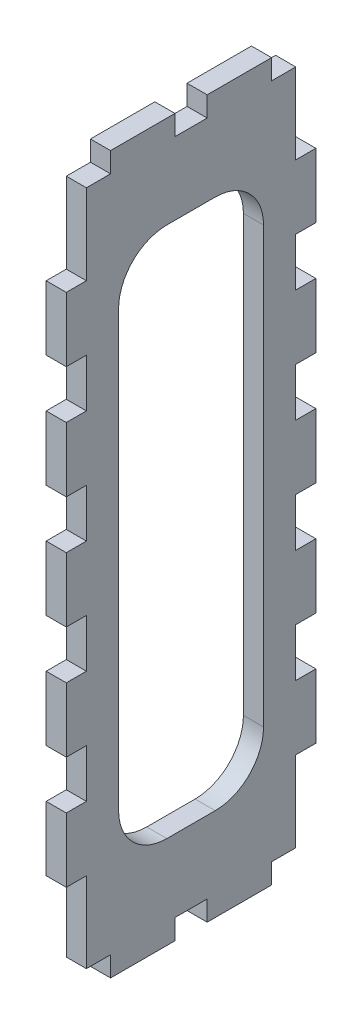
SolidWorks part; units mm, degrees
ref_plane "Front Plane" through (0, 0, 0) normal (0, 0, 1) x (1, 0, 0)
ref_plane "Top Plane" through (0, 0, 0) normal (0, 1, 0) x (1, 0, 0)
ref_plane "Right Plane" through (0, 0, 0) normal (1, 0, 0) x (0, 0, -1)
sketch "Sketch1" plane through (0, 0, 0) normal (1, 0, 0) x (0, 0, -1)
  line L0 (4.0513, 39.2766) -> (-3.5687, 39.2766)
  line L1 (-16.2687, 50.7066) -> (16.7513, 50.7066)
  line L2 (-16.2687, 50.7066) -> (-16.2687, -55.9734)
  line L3 (-16.2687, -55.9734) -> (16.7513, -55.9734)
  line L4 (16.7513, 50.7066) -> (16.7513, -55.9734)
  line L5 (-11.1887, 31.6566) -> (-11.1887, -36.9234)
  line L6 (11.6713, 31.6566) -> (11.6713, -36.9234)
  line L7 (4.0513, -44.5434) -> (-3.5687, -44.5434)
  line L8 (0.2413, 50.7066) -> (0.2413, 39.2766) construction
  line L9 (0.2413, -44.5434) -> (0.2413, -55.9734) construction
  line L10 (-16.2687, -2.6334) -> (-11.1887, -2.6334) construction
  line L11 (11.6713, -2.6334) -> (16.7513, -2.6334) construction
  arc A0 (-3.5687, 39.2766) -> (-11.1887, 31.6566) centre (-3.5687, 31.6566) ccw
  arc A1 (11.6713, 31.6566) -> (4.0513, 39.2766) centre (4.0513, 31.6566) ccw
  arc A2 (4.0513, -44.5434) -> (11.6713, -36.9234) centre (4.0513, -36.9234) ccw
  arc A3 (-11.1887, -36.9234) -> (-3.5687, -44.5434) centre (-3.5687, -36.9234) ccw
  dimension "D1" = 106.68
  dimension "D2" = 33.02
extrude "Boss-Extrude1" add sketch "Sketch1" along normal blind 3.175
sketch "Sketch2" plane through (0, 0, 0) normal (-1, 0, 0) x (0, 0, 1)
  line L0 (16.2687, 50.7066) -> (16.2687, 38.0066) construction
  line L1 (16.2687, 50.7066) -> (16.2687, -55.9734) construction
  dimension "D1" = 12.7
sketch "Sketch3" plane through (0, 0, 16.2687) normal (0, 0, 1) x (1, 0, 0)
  line L0 (3.175, 50.7066) -> (3.175, -55.9734) construction
  line L1 (0, 38.0066) -> (3.175, 38.0066)
  line L2 (0, 38.0066) -> (0, 27.8466)
  line L3 (0, 27.8466) -> (3.175, 27.8466)
  line L4 (3.175, 38.0066) -> (3.175, 27.8466)
  dimension "D1" = 10.16
extrude "Boss-Extrude2" add sketch "Sketch3" along normal blind 3.175
pattern_linear "LPattern1" count 5 spacing 17.78 along (0, -1, 0) of "Boss-Extrude2"
ref_plane "Plane1" through (0, 0, -0.2413) normal (0, 0, -1) x (-1, 0, 0)
mirror "Mirror1" about plane through (0, 0, -0.2413) normal (0, 0, -1) of "LPattern1", "Boss-Extrude2"
ref_plane "Plane3" through (0, -2.6334, 0) normal (0, 1, 0) x (1, 0, 0)
sketch "Sketch4" plane through (0, 50.7066, 0) normal (0, 1, 0) x (1, 0, 0)
  line L0 (0, -16.2687) -> (0, -12.4587) construction
  line L1 (0, 16.7513) -> (0, -16.2687) construction
  line L2 (0, 16.7513) -> (0, 12.9413) construction
  line L3 (3.175, 16.7513) -> (3.175, -16.2687) construction
  line L4 (0, -12.4587) -> (3.175, -12.4587)
  line L5 (0, -12.4587) -> (0, -2.2987)
  line L6 (0, -2.2987) -> (3.175, -2.2987)
  line L7 (3.175, -12.4587) -> (3.175, -2.2987)
  dimension "D1" = 3.81
  dimension "D2" = 3.81
  dimension "D3" = 10.16
extrude "Boss-Extrude3" add sketch "Sketch4" along normal blind 3.175
mirror "Mirror2" about plane through (0, 0, -0.2413) normal (0, 0, -1) of "Boss-Extrude3"
mirror "Mirror3" about plane through (0, -2.6334, 0) normal (0, 1, 0) of "Mirror2", "Boss-Extrude3"
